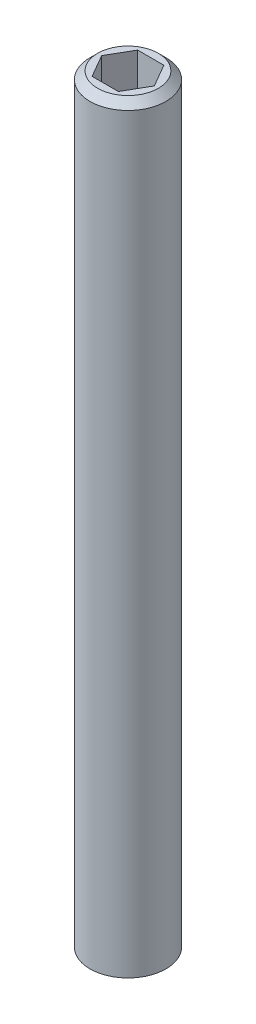
SolidWorks part; units mm, degrees
ref_plane "Front Plane" through (0, 0, 0) normal (0, 0, 1) x (1, 0, 0)
ref_plane "Top Plane" through (0, 0, 0) normal (0, 1, 0) x (1, 0, 0)
ref_plane "Right Plane" through (0, 0, 0) normal (1, 0, 0) x (0, 0, -1)
sketch "Sketch1" plane through (0, 0, 0) normal (0, 1, 0) x (1, 0, 0)
  circle A0 centre (0, 0) radius 1.25
  dimension "D1" = 2.5
extrude "Boss-Extrude1" add sketch "Sketch1" along normal blind 25
sketch "Sketch2" plane through (0, 25, 0) normal (0, 1, 0) x (1, 0, 0)
  line L1 (0.866, 0) -> (0.433, 0.75)
  line L2 (0.433, 0.75) -> (-0.433, 0.75)
  line L3 (-0.433, 0.75) -> (-0.866, 0)
  line L4 (-0.866, 0) -> (-0.433, -0.75)
  line L5 (-0.433, -0.75) -> (0.433, -0.75)
  line L6 (0.433, -0.75) -> (0.866, 0)
  circle A0 centre (0, 0) radius 0.75 construction
  dimension "D1" = 1.5
extrude "Cut-Extrude1" cut sketch "Sketch2" against normal blind 2
chamfer "Chamfer1" distance 0.25 angle 45 1 edges at (0, 25, 1.25)
